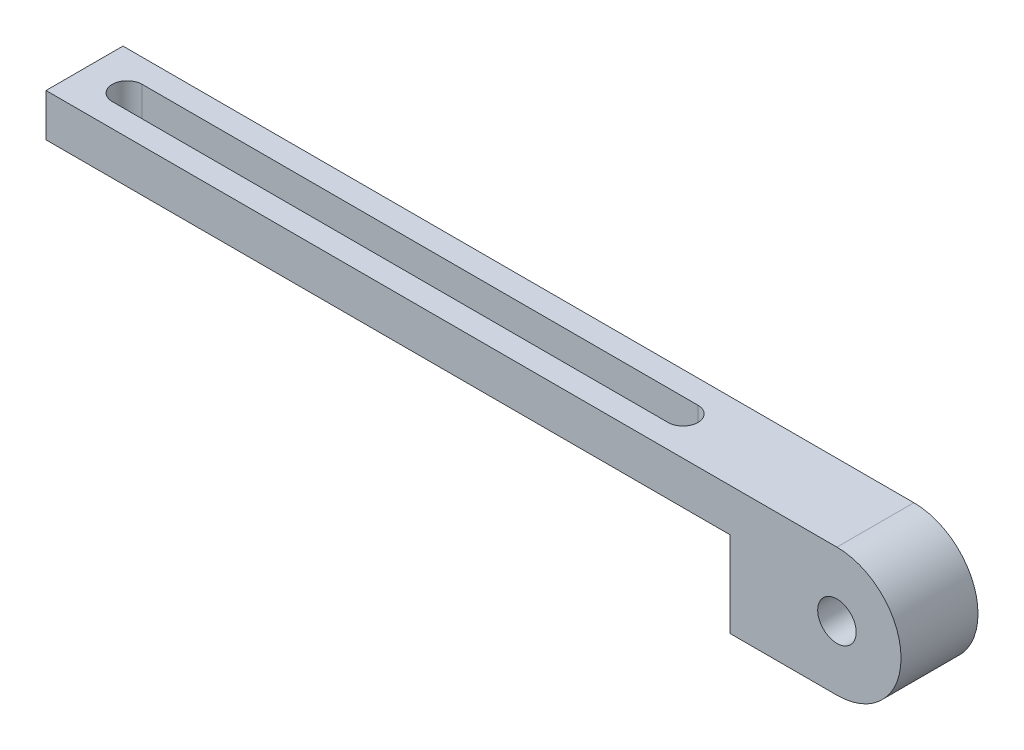
SolidWorks part; units mm, degrees
ref_plane "Front Plane" through (0, 0, 0) normal (0, 0, 1) x (1, 0, 0)
ref_plane "Top Plane" through (0, 0, 0) normal (0, 1, 0) x (1, 0, 0)
ref_plane "Right Plane" through (0, 0, 0) normal (1, 0, 0) x (0, 0, -1)
sketch "Sketch1" plane through (0, 0, 0) normal (0, 1, 0) x (1, 0, 0)
  line L1 (0, 0) -> (100, 0)
  line L2 (0, 0) -> (0, 9)
  line L3 (0, 9) -> (100, 9)
  line L4 (100, 0) -> (100, 9)
  dimension "D1" = 9
  dimension "D2" = 100
extrude "Boss-Extrude1" add sketch "Sketch1" along normal blind 5
sketch "Sketch2" plane through (0, 5, 0) normal (0, 1, 0) x (1, 0, 0)
  line L0 (0, 4.5) -> (100, 4.5) construction
  line L1 (0, 9) -> (0, 0) construction
  line L2 (100, 0) -> (100, 9) construction
  line L3 (5, 4.5) -> (70, 4.5) construction
  line L4 (5, 6.25) -> (70, 6.25)
  line L5 (5, 2.75) -> (70, 2.75)
  arc A0 (5, 6.25) -> (5, 2.75) centre (5, 4.5) ccw
  arc A1 (70, 2.75) -> (70, 6.25) centre (70, 4.5) ccw
  point P8 (37.5, 4.5)
  dimension "D1" = 3.5
  dimension "D2" = 5
  dimension "D3" = 30
extrude "Cut-Extrude1" cut sketch "Sketch2" against normal through all
sketch "Sketch3" plane through (0, 0, -9) normal (0, 0, -1) x (-1, 0, 0)
  line L1 (-100, 5) -> (-80, 5)
  line L2 (-100, 5) -> (-100, -10)
  line L3 (-100, -10) -> (-80, -10)
  line L4 (-80, 5) -> (-80, -10)
  dimension "D1" = 15
  dimension "D2" = 20
extrude "Boss-Extrude2" add sketch "Sketch3" against normal up to surface (9 mm away) up to face at (50, 2.5, 0)
sketch "Sketch4" plane through (0, 0, -9) normal (0, 0, -1) x (-1, 0, 0)
  line L0 (-100, -2.5) -> (-80, -2.5) construction
  line L1 (-100, 5) -> (-100, -10) construction
  line L2 (-80, -10) -> (-80, 0) construction
  line L4 (-100, 5) -> (0, 5) construction
  line L5 (-92.5, -10) -> (-100, -10)
  line L6 (-100, -10) -> (-100, 5)
  line L7 (-100, 5) -> (-92.5, 5)
  line L8 (-100, -10) -> (-80, -10) construction
  arc A1 (-92.5, -10) -> (-92.5, 5) centre (-92.5, -2.5) cw
  circle A2 centre (-92.5, -2.5) radius 2.25
  line M5 (0, 5) -> (-100, 5)
  line M6 (-100, 5) -> (-100, -10)
  line M7 (-100, -10) -> (-80, -10)
  dimension "D1" = 4.5
extrude "Cut-Extrude2" cut sketch "Sketch4" against normal blind 10 contours A1 L6 M7 | A1 M6 M5 | A2 L0
